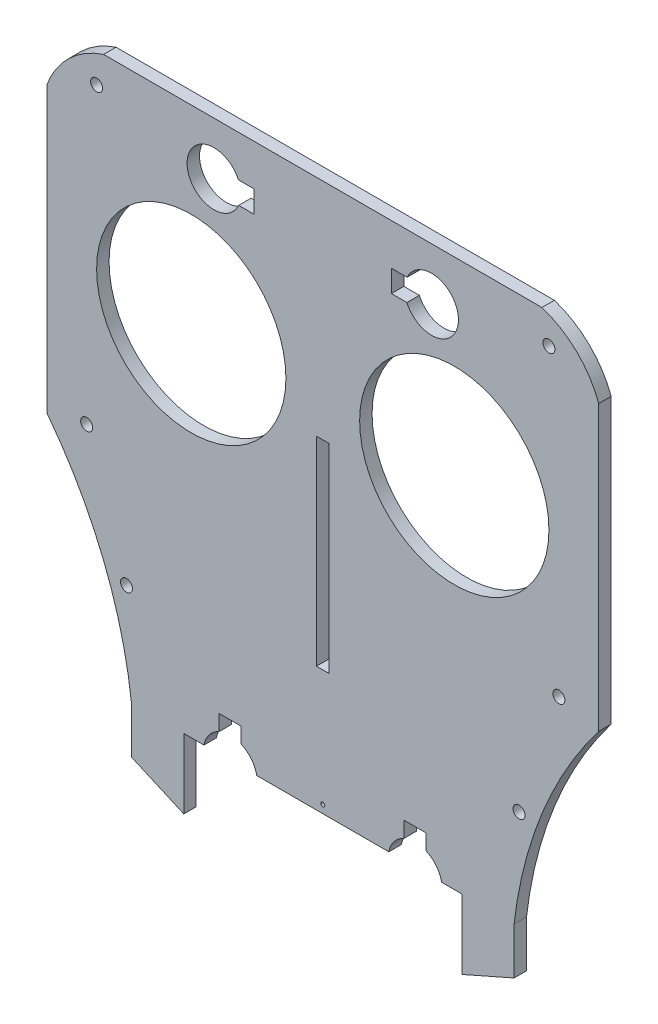
SolidWorks part; units mm, degrees
ref_plane "Front Plane" through (0, 0, 0) normal (0, 0, 1) x (1, 0, 0)
ref_plane "Top Plane" through (0, 0, 0) normal (0, 1, 0) x (1, 0, 0)
ref_plane "Right Plane" through (0, 0, 0) normal (1, 0, 0) x (0, 0, -1)
sketch "Sketch1" plane through (0, 0, 0) normal (0, 0, 1) x (1, 0, 0)
  line L0 (70.358, 0) -> (-70.358, 0)
  line L1 (-70.358, 0) -> (-70.358, -139.7)
  line L4 (-70.358, -139.7) -> (70.358, -139.7)
  line L5 (0, 0) -> (0, -139.7) construction
  line L8 (70.358, 0) -> (70.358, -139.7)
  dimension "D1" = 70.358
  dimension "D2" = 139.7
  dimension "D5" = 140.716
extrude "main body" add sketch "Sketch1" along normal blind 3.175
sketch "Sketch2" plane through (0, 0, 3.175) normal (0, 0, 1) x (1, 0, 0)
  line L0 (70.358, 0) -> (-70.358, 0) construction
  line L2 (-70.358, -139.7) -> (70.358, -139.7) construction
  line L3 (0, 0) -> (0, -139.7) construction
  circle A0 centre (-33.528, -48.26) radius 24.13
  point P71 (-52.324, -48.26)
  point P86 (-3.556, -48.26)
  point P87 (-3.556, -48.26)
  line B0 (-17.5006, -13.3191) -> (-17.5006, -10.5251)
  line B1 (-17.5006, -10.5251) -> (-21.4966, -10.5251)
  line B2 (-21.4513, -16.1131) -> (-17.5006, -16.1131)
  line B3 (-17.5006, -16.1131) -> (-17.5006, -13.3191)
  arc B4 (-21.4966, -10.5251) -> (-21.4513, -16.1131) centre (-27.7368, -13.3699) ccw
  dimension "D3" = 33.528
  dimension "D6" = 48.26
  dimension "D2" = 48.26
sketch_block_instance "Block2-3"
sketch_block "Block2"
extrude "cuts for eyes and motors" cut sketch "Sketch2" against normal through all
sketch "Sketch4" plane through (0, 0, 3.175) normal (0, 0, 1) x (1, 0, 0)
  line L0 (0, 0) -> (0, -139.7) construction
  line L1 (-70.358, -139.7) -> (70.358, -139.7) construction
  line L2 (0, -57.15) -> (0, -107.95) construction
  line L3 (-1.6129, -57.15) -> (1.6129, -57.15)
  line L4 (-1.6129, -57.15) -> (-1.6129, -107.95)
  line L5 (-1.6129, -107.95) -> (1.6129, -107.95)
  line L6 (1.6129, -57.15) -> (1.6129, -107.95)
  line L7 (70.358, 0) -> (-70.358, 0) construction
  dimension "D1" = 3.2258
  dimension "D2" = 50.8
  dimension "D3" = 57.15
extrude "cut for nose" cut sketch "Sketch4" against normal through all
mirror "Mirror1" about plane through (0, 0, 0) normal (1, 0, 0) of "cuts for eyes and motors"
sketch "Sketch11" plane through (0, 0, 3.175) normal (0, 0, 1) x (1, 0, 0)
  line L0 (-70.358, -139.7) -> (-70.358, -86.36)
  line L1 (-70.358, 0) -> (-70.358, -139.7) construction
  line L4 (-70.358, 0) -> (-70.358, -13.97)
  line L5 (-70.358, 0) -> (-55.88, 0)
  line L6 (70.358, 0) -> (-70.358, 0) construction
  line L8 (-70.358, -139.7) -> (70.358, -139.7) construction
  line L9 (-70.358, -139.7) -> (-48.768, -139.7)
  arc A0 (-70.358, -86.36) -> (-48.768, -139.7) centre (-156.0073, -152.067) cw
  arc A1 (-70.358, -13.97) -> (-55.88, 0) centre (-48.7264, -21.9009) cw
  dimension "D1" = 21.59
  dimension "D2" = 53.34
  dimension "D3" = 13.97
  dimension "D4" = 14.478
extrude "cut for rounded face features" cut sketch "Sketch11" against normal through all
mirror "mirror of rounded feature" about plane through (0, 0, 0) normal (1, 0, 0) of "cut for rounded face features"
sketch "Sketch12" plane through (0, 0, 3.175) normal (0, 0, 1) x (1, 0, 0)
  line L0 (-70.358, -13.97) -> (-70.358, -86.36) construction
  line L1 (55.88, 0) -> (-55.88, 0) construction
  circle A0 centre (-57.658, -7.62) radius 1.524
  circle A1 centre (-60.198, -83.82) radius 1.524
  circle A2 centre (-50.038, -114.3) radius 1.524
  dimension "D1" = 3.048
  dimension "D2" = 3.048
  dimension "D3" = 3.048
  dimension "D4" = 10.16
  dimension "D5" = 12.7
  dimension "D6" = 114.3
  dimension "D7" = 20.32
  dimension "D8" = 7.62
  dimension "D9" = 83.82
extrude "holes for spacers" cut sketch "Sketch12" against normal through all
mirror "mirror of spacer hole" about plane through (0, 0, 0) normal (1, 0, 0) of "holes for spacers"
sketch "Sketch14" plane through (0, 0, 3.175) normal (0, 0, 1) x (1, 0, 0)
  line L0 (-48.768, -139.7) -> (-35.433, -139.7)
  line L1 (-48.768, -139.7) -> (48.768, -139.7) construction
  line L2 (-35.433, -139.7) -> (-35.433, -157.48)
  line L3 (-35.433, -157.48) -> (-48.768, -151.5961)
  line L4 (-48.768, -151.5961) -> (-48.768, -139.7)
  dimension "D1" = 13.335
  dimension "D2" = 17.78
extrude "Boss-Extrude1" add sketch "Sketch14" against normal blind 3.175
mirror "Mirror3" about plane through (0, 0, 0) normal (1, 0, 0) of "Boss-Extrude1"
sketch "Sketch15" plane through (0, 0, 3.175) normal (0, 0, 1) x (1, 0, 0)
  line B0 (-23.622, -130.7846) -> (-26.416, -130.7846)
  line B1 (-26.416, -130.7846) -> (-26.416, -134.7807)
  line B2 (-20.828, -134.7353) -> (-20.828, -130.7846)
  line B3 (-20.828, -130.7846) -> (-23.622, -130.7846)
  arc B4 (-26.416, -134.7807) -> (-20.828, -134.7353) centre (-23.5712, -141.0208) ccw
  line B5 (23.5204, -130.7846) -> (20.7264, -130.7846)
  line B6 (20.7264, -130.7846) -> (20.7264, -134.7807)
  line B7 (26.3144, -134.7353) -> (26.3144, -130.7846)
  line B8 (26.3144, -130.7846) -> (23.5204, -130.7846)
  arc B9 (20.7264, -134.7807) -> (26.3144, -134.7353) centre (23.5712, -141.0208) ccw
sketch_block_instance "servo_topAperture_SG90-1"
sketch_block_instance "Block2-5"
extrude "Cut-Extrude1" cut sketch "Sketch15" against normal through all
sketch "Sketch16" plane through (0, 0, 3.175) normal (0, 0, 1) x (1, 0, 0)
  line L1 (-16.8416, -139.7) -> (16.8416, -139.7) construction
  circle A0 centre (0, -137.668) radius 0.508
  dimension "D1" = 1.016
  dimension "D3" = 2.032
extrude "Cut-Extrude2" cut sketch "Sketch16" against normal through all
